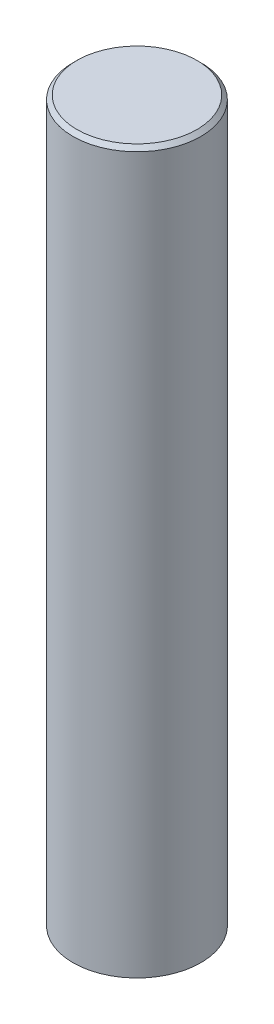
SolidWorks part; units mm, degrees
ref_plane "Front Plane" through (0, 0, 0) normal (0, 0, 1) x (1, 0, 0)
ref_plane "Top Plane" through (0, 0, 0) normal (0, 1, 0) x (1, 0, 0)
ref_plane "Right Plane" through (0, 0, 0) normal (1, 0, 0) x (0, 0, -1)
sketch "Sketch1" plane through (0, 0, 0) normal (0, 1, 0) x (1, 0, 0)
  circle A0 centre (0, 0) radius 16
  dimension "D1" = 32
extrude "Boss-Extrude1" add sketch "Sketch1" along normal blind 180
chamfer "Chamfer1" distance 1 angle 45 1 edges at (0, 180, 16)
